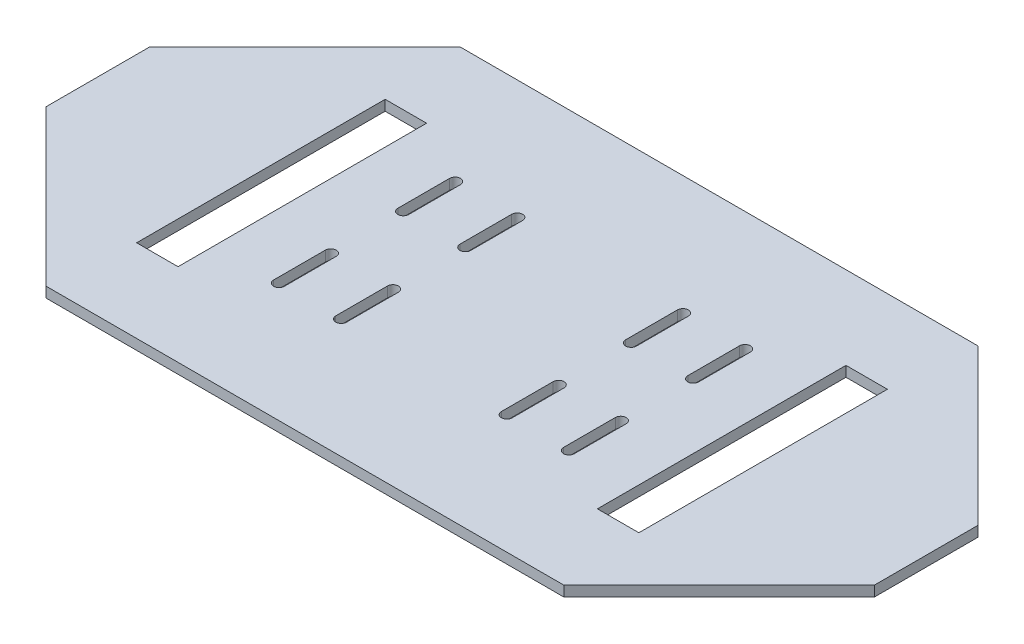
SolidWorks part; units mm, degrees
material "Pin"
ref_plane "Plan de face" through (0, 0, 0) normal (0, 0, 1) x (1, 0, 0)
ref_plane "Plan de dessus" through (0, 0, 0) normal (0, 1, 0) x (1, 0, 0)
ref_plane "Plan de droite" through (0, 0, 0) normal (1, 0, 0) x (0, 0, -1)
sketch "Esquisse1" plane through (0, 0, 0) normal (0, 1, 0) x (1, 0, 0)
  line L1 (0, 0) -> (160, 0)
  line L2 (0, 0) -> (0, 80)
  line L3 (0, 80) -> (160, 80)
  line L4 (160, 0) -> (160, 80)
  dimension "D1" = 80
  dimension "D2" = 160
extrude "Boss.-Extru.1" add sketch "Esquisse1" along normal blind 2
sketch "Esquisse2" plane through (0, 2, 0) normal (0, 1, 0) x (1, 0, 0)
  line L0 (0, 50) -> (30, 80)
  line L1 (0, 80) -> (0, 0) construction
  line L2 (160, 80) -> (0, 80) construction
  line L3 (130, 80) -> (160, 50)
  line L4 (160, 0) -> (160, 80) construction
  line L5 (130, 0) -> (160, 30)
  line L6 (0, 0) -> (160, 0) construction
  line L7 (0, 30) -> (30, 0)
  line L8 (0, 80) -> (30, 80)
  line L9 (0, 30) -> (0, 0)
  line L10 (0, 0) -> (30, 0)
  line L11 (130, 0) -> (160, 0)
  line L12 (160, 0) -> (160, 30)
  line L13 (160, 50) -> (160, 80)
  line L14 (160, 80) -> (130, 80)
  line L15 (0, 80) -> (0, 50)
  dimension "D1" = 30
  dimension "D2" = 30
  dimension "D3" = 30
  dimension "D4" = 30
  dimension "D5" = 30
  dimension "D6" = 30
  dimension "D7" = 30
  dimension "D8" = 30
extrude "Enlèv. mat.-Extru.2" cut sketch "Esquisse2" against normal blind 2
sketch "Esquisse7" plane through (0, 2, 0) normal (0, 1, 0) x (1, 0, 0)
  line L0 (64, 23) -> (64, 33) construction
  line L1 (62.95, 23) -> (62.95, 33)
  line L2 (65.05, 23) -> (65.05, 33)
  line L3 (52, 23) -> (52, 33) construction
  line L4 (50.95, 23) -> (50.95, 33)
  line L5 (53.05, 23) -> (53.05, 33)
  line L6 (3.5692, 40) -> (183.2325, 40) construction
  line L7 (52, 47) -> (52, 57) construction
  line L8 (50.95, 47) -> (50.95, 57)
  line L9 (53.05, 47) -> (53.05, 57)
  line L10 (64, 47) -> (64, 57) construction
  line L11 (62.95, 47) -> (62.95, 57)
  line L12 (65.05, 47) -> (65.05, 57)
  line L13 (30, 0) -> (130, 0) construction
  line L14 (80, -22.0489) -> (80, 126.4706) construction
  line L15 (0, 50) -> (0, 30) construction
  line L16 (96, 47) -> (96, 57) construction
  line L17 (97.05, 47) -> (97.05, 57)
  line L18 (94.95, 47) -> (94.95, 57)
  line L19 (108, 47) -> (108, 57) construction
  line L20 (109.05, 47) -> (109.05, 57)
  line L21 (106.95, 47) -> (106.95, 57)
  line L22 (108, 23) -> (108, 33) construction
  line L23 (109.05, 23) -> (109.05, 33)
  line L24 (106.95, 23) -> (106.95, 33)
  line L25 (96, 23) -> (96, 33) construction
  line L26 (97.05, 23) -> (97.05, 33)
  line L27 (94.95, 23) -> (94.95, 33)
  arc A0 (62.95, 23) -> (65.05, 23) centre (64, 23) ccw
  arc A1 (65.05, 33) -> (62.95, 33) centre (64, 33) ccw
  arc A2 (50.95, 23) -> (53.05, 23) centre (52, 23) ccw
  arc A3 (53.05, 33) -> (50.95, 33) centre (52, 33) ccw
  arc A4 (50.95, 47) -> (53.05, 47) centre (52, 47) ccw
  arc A5 (53.05, 57) -> (50.95, 57) centre (52, 57) ccw
  arc A6 (62.95, 47) -> (65.05, 47) centre (64, 47) ccw
  arc A7 (65.05, 57) -> (62.95, 57) centre (64, 57) ccw
  arc A8 (97.05, 47) -> (94.95, 47) centre (96, 47) cw
  arc A9 (94.95, 57) -> (97.05, 57) centre (96, 57) cw
  arc A10 (109.05, 47) -> (106.95, 47) centre (108, 47) cw
  arc A11 (106.95, 57) -> (109.05, 57) centre (108, 57) cw
  arc A12 (109.05, 23) -> (106.95, 23) centre (108, 23) cw
  arc A13 (106.95, 33) -> (109.05, 33) centre (108, 33) cw
  arc A14 (97.05, 23) -> (94.95, 23) centre (96, 23) cw
  arc A15 (94.95, 33) -> (97.05, 33) centre (96, 33) cw
  point P2 (64, 28)
  point P7 (52, 28)
  point P18 (52, 52)
  point P23 (64, 52)
  point P38 (96, 52)
  point P45 (108, 52)
  point P52 (108, 28)
  point P59 (96, 28)
  dimension "D1" = 12
  dimension "D2" = 24
  dimension "D3" = 2.1
  dimension "D4" = 2.1
  dimension "D5" = 2.1
  dimension "D6" = 2.1
  dimension "D7" = 12
  dimension "D8" = 24
  dimension "D9" = 10
  dimension "D10" = 10
  dimension "D11" = 10
  dimension "D12" = 10
  dimension "D13" = 12
  dimension "D14" = 12
  dimension "D15" = 40
  dimension "D16" = 80
  dimension "D17" = 16
extrude "Enlèv. mat.-Extru.3" cut sketch "Esquisse7" against normal blind 2
sketch "Esquisse8" plane through (0, 2, 0) normal (0, 1, 0) x (1, 0, 0)
  line L0 (30, 0) -> (130, 0) construction
  line L1 (128.5, 16) -> (120.5, 16)
  line L2 (128.5, 16) -> (128.5, 64)
  line L3 (128.5, 64) -> (120.5, 64)
  line L4 (120.5, 16) -> (120.5, 64)
  line L5 (130, 80) -> (30, 80) construction
  line L6 (160, 30) -> (160, 50) construction
  line L7 (80, -18.8233) -> (80, 100.9903) construction
  line L8 (31.5, 64) -> (39.5, 64)
  line L9 (39.5, 16) -> (39.5, 64)
  line L10 (31.5, 16) -> (39.5, 16)
  line L11 (31.5, 16) -> (31.5, 64)
  dimension "D1" = 16
  dimension "D2" = 16
  dimension "D3" = 8
  dimension "D4" = 31.5
  dimension "D5" = 80
extrude "Enlèv. mat.-Extru.4" cut sketch "Esquisse8" against normal up to next
